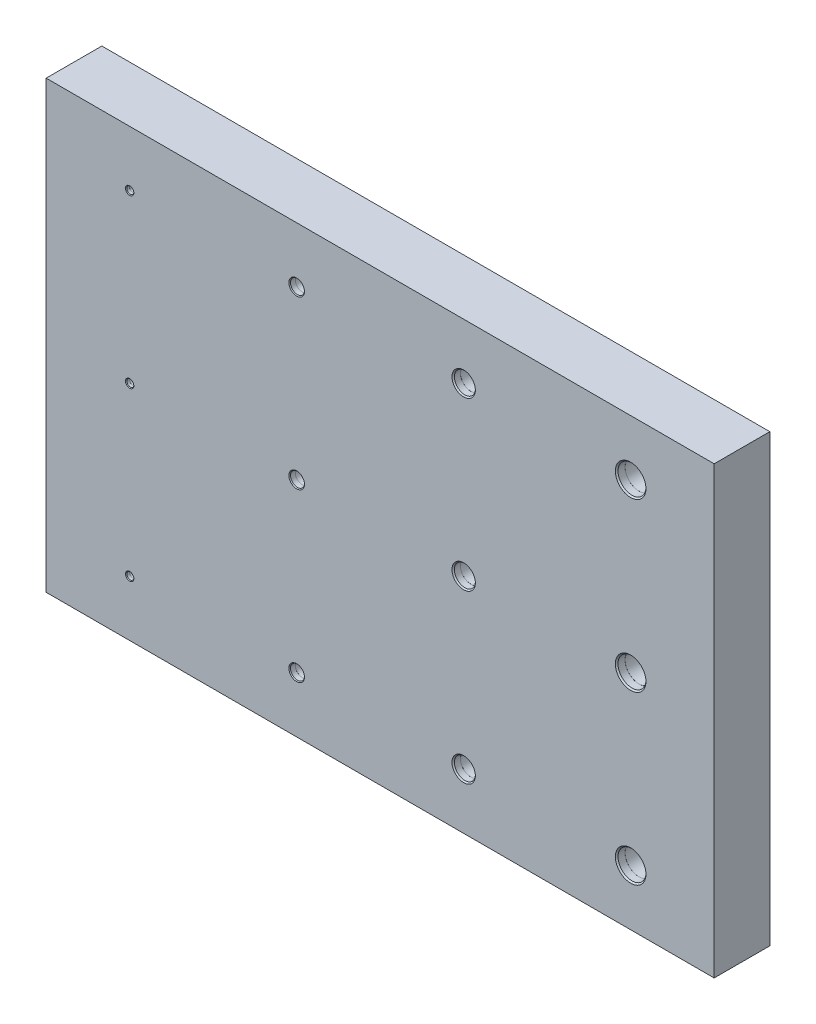
SolidWorks part; units mm, degrees
material "6061-T6 Al"
ref_plane "Front" through (0, 0, 0) normal (0, 0, 1) x (1, 0, 0)
ref_plane "Top" through (0, 0, 0) normal (0, 1, 0) x (1, 0, 0)
ref_plane "Right" through (0, 0, 0) normal (1, 0, 0) x (0, 0, -1)
sketch "Sketch1" plane through (0, 0, 0) normal (0, 0, 1) x (1, 0, 0)
  line L1 (0, 0) -> (304.8, 0)
  line L2 (0, 0) -> (0, 203.2)
  line L3 (0, 203.2) -> (304.8, 203.2)
  line L4 (304.8, 0) -> (304.8, 203.2)
  dimension "D1" = 203.2
  dimension "D2" = 304.8
extrude "Boss-Extrude1" add sketch "Sketch1" along normal blind 25.4
hole_wizard "3/32 (0.09375) Diameter Hole1" positions "Sketch3" profile "Sketch2" hole size "3/32" standard "Ansi Inch" end condition through all
sketch "Sketch3" plane through (0, 0, 25.4) normal (0, 0, 1) x (1, 0, 0)
  line L0 (38.1, 177.8) -> (114.3, 177.8) construction
  line L1 (114.3, 177.8) -> (190.5, 177.8) construction
  line L2 (190.5, 177.8) -> (266.7, 177.8) construction
  line L3 (38.1, 177.8) -> (38.1, 101.6) construction
  line L4 (114.3, 177.8) -> (114.3, 101.6) construction
  line L5 (190.5, 177.8) -> (190.5, 101.6) construction
  line L6 (266.7, 177.8) -> (266.7, 101.6) construction
  line L7 (38.1, 101.6) -> (114.3, 101.6) construction
  line L8 (114.3, 101.6) -> (190.5, 101.6) construction
  line L9 (190.5, 101.6) -> (266.7, 101.6) construction
  line L10 (38.1, 101.6) -> (38.1, 25.4) construction
  line L11 (114.3, 101.6) -> (114.3, 25.4) construction
  line L12 (190.5, 101.6) -> (190.5, 25.4) construction
  line L13 (266.7, 101.6) -> (266.7, 25.4) construction
  line L14 (38.1, 25.4) -> (114.3, 25.4) construction
  line L15 (114.3, 25.4) -> (190.5, 25.4) construction
  line L16 (190.5, 25.4) -> (266.7, 25.4) construction
  line L17 (0, 101.6) -> (38.1, 101.6) construction
  line L18 (0, 203.2) -> (0, 0) construction
  line L19 (152.4, 177.8) -> (152.4, 203.2) construction
  line L20 (304.8, 203.2) -> (0, 203.2) construction
  point P0 (38.1, 177.8)
  point P1 (38.1, 101.6)
  point P3 (38.1, 25.4)
  point P5 (114.3, 177.8)
  point P7 (114.3, 101.6)
  point P9 (114.3, 25.4)
  point P11 (190.5, 177.8)
  point P13 (190.5, 101.6)
  point P15 (190.5, 25.4)
  point P17 (266.7, 177.8)
  point P19 (266.7, 101.6)
  point P21 (266.7, 25.4)
  dimension "D1" = 76.2
  dimension "D2" = 76.2
sketch "Sketch2" plane through (38.1, 177.8, 25.4) normal (1, 0, 0) x (0, -1, 0)
  line L0 (0, 0) -> (0, 25.4)
  line L1 (0, 25.4) -> (1.1906, 25.4)
  line L2 (1.1906, 25.4) -> (1.1906, 0)
  line L5 (1.1906, 0) -> (0, 0)
  line L11 (0, -6.35) -> (0, 107.95) construction
  dimension "Thru Hole Dia." = 2.3812
  dimension "Thru Hole Depth" = 25.4
hole_wizard "CBORE for #4 Socket Head Cap Screw1" positions "Sketch5" profile "Sketch4" counterbore size "#4" standard "Ansi Inch"
sketch "Sketch5" plane through (0, 0, 25.4) normal (0, 0, 1) x (1, 0, 0)
  point P0 (38.1, 177.8)
  point P1 (38.1, 101.6)
  point P3 (38.1, 25.4)
sketch "Sketch4" plane through (38.1, 177.8, 25.4) normal (1, 0, 0) x (0, -1, 0)
  line L0 (0, 0) -> (0, 7.3039)
  line L1 (0, 7.3039) -> (1.5875, 6.35)
  line L2 (1.5875, 6.35) -> (1.5875, 1.524)
  line L3 (1.5875, 1.524) -> (1.6002, 1.524)
  line L5 (1.6002, 1.524) -> (1.6002, 0.3048)
  line L6 (1.6002, 0.3048) -> (1.905, 0)
  line L7 (1.905, 0) -> (0, 0)
  line L8 (-1.6002, 0.3048) -> (-1.905, 0) construction
  line L10 (0, 7.3039) -> (-1.5875, 6.35) construction
  line L11 (0, -6.35) -> (0, 107.95) construction
  dimension "Hole Dia." = 3.175
  dimension "Hole Depth" = 6.35
  dimension "C'Bore Dia." = 3.2004
  dimension "C'Bore Depth" = 1.524
  dimension "Near C'Sink Dia." = 3.81
  dimension "Near C'Sink Angle" = 90
  dimension "Drill Angle" = 118
hole_wizard "CBORE for 1/4 Socket Head Cap Screw1" positions "Sketch7" profile "Sketch6" counterbore size "1/4" standard "Ansi Inch"
sketch "Sketch7" plane through (0, 0, 25.4) normal (0, 0, 1) x (1, 0, 0)
  point P0 (114.3, 177.8)
  point P1 (114.3, 101.6)
  point P3 (114.3, 25.4)
sketch "Sketch6" plane through (114.3, 177.8, 25.4) normal (1, 0, 0) x (0, -1, 0)
  line L0 (0, 0) -> (0, 11.4327)
  line L1 (0, 11.4327) -> (3.175, 9.525)
  line L2 (3.175, 9.525) -> (3.175, 2.54)
  line L3 (3.175, 2.54) -> (3.1877, 2.54)
  line L5 (3.1877, 2.54) -> (3.1877, 0.3683)
  line L6 (3.1877, 0.3683) -> (3.556, 0)
  line L7 (3.556, 0) -> (0, 0)
  line L8 (-3.1877, 0.3683) -> (-3.556, 0) construction
  line L10 (0, 11.4327) -> (-3.175, 9.525) construction
  line L11 (0, -6.35) -> (0, 107.95) construction
  dimension "Hole Dia." = 6.35
  dimension "Hole Depth" = 9.525
  dimension "C'Bore Dia." = 6.3754
  dimension "C'Bore Depth" = 2.54
  dimension "Near C'Sink Dia." = 7.112
  dimension "Near C'Sink Angle" = 90
  dimension "Drill Angle" = 118
hole_wizard "CBORE for 3/8 Socket Head Cap Screw1" positions "Sketch9" profile "Sketch8" counterbore size "3/8" standard "Ansi Inch"
sketch "Sketch9" plane through (0, 0, 25.4) normal (0, 0, 1) x (1, 0, 0)
  point P0 (190.5, 177.8)
  point P1 (190.5, 101.6)
  point P3 (190.5, 25.4)
sketch "Sketch8" plane through (190.5, 177.8, 25.4) normal (1, 0, 0) x (0, -1, 0)
  line L0 (0, 0) -> (0, 18.1016)
  line L1 (0, 18.1016) -> (4.7625, 15.24)
  line L2 (4.7625, 15.24) -> (4.7625, 3.302)
  line L3 (4.7625, 3.302) -> (4.7879, 3.302)
  line L5 (4.7879, 3.302) -> (4.7879, 0.5461)
  line L6 (4.7879, 0.5461) -> (5.334, 0)
  line L7 (5.334, 0) -> (0, 0)
  line L8 (-4.7879, 0.5461) -> (-5.334, 0) construction
  line L10 (0, 18.1016) -> (-4.7625, 15.24) construction
  line L11 (0, -6.35) -> (0, 107.95) construction
  dimension "Hole Dia." = 9.525
  dimension "Hole Depth" = 15.24
  dimension "C'Bore Dia." = 9.5758
  dimension "C'Bore Depth" = 3.302
  dimension "Near C'Sink Dia." = 10.668
  dimension "Near C'Sink Angle" = 90
  dimension "Drill Angle" = 118
hole_wizard "CBORE for 1/2 Socket Head Cap Screw1" positions "Sketch11" profile "Sketch10" counterbore size "1/2" standard "Ansi Inch"
sketch "Sketch11" plane through (0, 0, 25.4) normal (0, 0, 1) x (1, 0, 0)
  point P0 (266.7, 177.8)
  point P1 (266.7, 101.6)
  point P3 (266.7, 25.4)
sketch "Sketch10" plane through (266.7, 177.8, 25.4) normal (1, 0, 0) x (0, -1, 0)
  line L0 (0, 0) -> (0, 22.8655)
  line L1 (0, 22.8655) -> (6.35, 19.05)
  line L2 (6.35, 19.05) -> (6.35, 3.81)
  line L3 (6.35, 3.81) -> (6.3754, 3.81)
  line L5 (6.3754, 3.81) -> (6.3754, 0.6096)
  line L6 (6.3754, 0.6096) -> (6.985, 0)
  line L7 (6.985, 0) -> (0, 0)
  line L8 (-6.3754, 0.6096) -> (-6.985, 0) construction
  line L10 (0, 22.8655) -> (-6.35, 19.05) construction
  line L11 (0, -6.35) -> (0, 107.95) construction
  dimension "Hole Dia." = 12.7
  dimension "Hole Depth" = 19.05
  dimension "C'Bore Dia." = 12.7508
  dimension "C'Bore Depth" = 3.81
  dimension "Near C'Sink Dia." = 13.97
  dimension "Near C'Sink Angle" = 90
  dimension "Drill Angle" = 118
hole_wizard "3/16 (0.1875) Diameter Hole1" positions "Sketch13" profile "Sketch12" hole size "3/16" standard "Ansi Inch" end condition through all
sketch "Sketch13" plane through (0, 0, 25.4) normal (0, 0, 1) x (1, 0, 0)
  point P0 (114.3, 177.8)
  point P1 (114.3, 101.6)
  point P4 (114.3, 25.4)
sketch "Sketch12" plane through (114.3, 177.8, 25.4) normal (1, 0, 0) x (0, -1, 0)
  line L0 (0, 0) -> (0, 25.4)
  line L1 (0, 25.4) -> (2.3812, 25.4)
  line L2 (2.3812, 25.4) -> (2.3812, 0)
  line L5 (2.3812, 0) -> (0, 0)
  line L11 (0, -6.35) -> (0, 107.95) construction
  dimension "Thru Hole Dia." = 4.7625
  dimension "Thru Hole Depth" = 25.4
hole_wizard "1/4 (0.25) Diameter Hole1" positions "Sketch15" profile "Sketch14" hole size "1/4" standard "Ansi Inch" end condition through all
sketch "Sketch15" plane through (0, 0, 25.4) normal (0, 0, 1) x (1, 0, 0)
  point P0 (190.5, 177.8)
  point P1 (190.5, 101.6)
  point P4 (190.5, 25.4)
sketch "Sketch14" plane through (190.5, 177.8, 25.4) normal (1, 0, 0) x (0, -1, 0)
  line L0 (0, 0) -> (0, 25.4)
  line L1 (0, 25.4) -> (3.175, 25.4)
  line L2 (3.175, 25.4) -> (3.175, 0)
  line L5 (3.175, 0) -> (0, 0)
  line L11 (0, -6.35) -> (0, 107.95) construction
  dimension "Thru Hole Dia." = 6.35
  dimension "Thru Hole Depth" = 25.4
hole_wizard "13/32 (0.40625) Diameter Hole1" positions "Sketch17" profile "Sketch16" hole size "13/32" standard "Ansi Inch" end condition through all
sketch "Sketch17" plane through (0, 0, 25.4) normal (0, 0, 1) x (1, 0, 0)
  point P0 (266.7, 177.8)
  point P1 (266.7, 101.6)
  point P4 (266.7, 25.4)
sketch "Sketch16" plane through (266.7, 177.8, 25.4) normal (1, 0, 0) x (0, -1, 0)
  line L0 (0, 0) -> (0, 25.4)
  line L1 (0, 25.4) -> (5.1594, 25.4)
  line L2 (5.1594, 25.4) -> (5.1594, 0)
  line L5 (5.1594, 0) -> (0, 0)
  line L11 (0, -6.35) -> (0, 107.95) construction
  dimension "Thru Hole Dia." = 10.3187
  dimension "Thru Hole Depth" = 25.4
